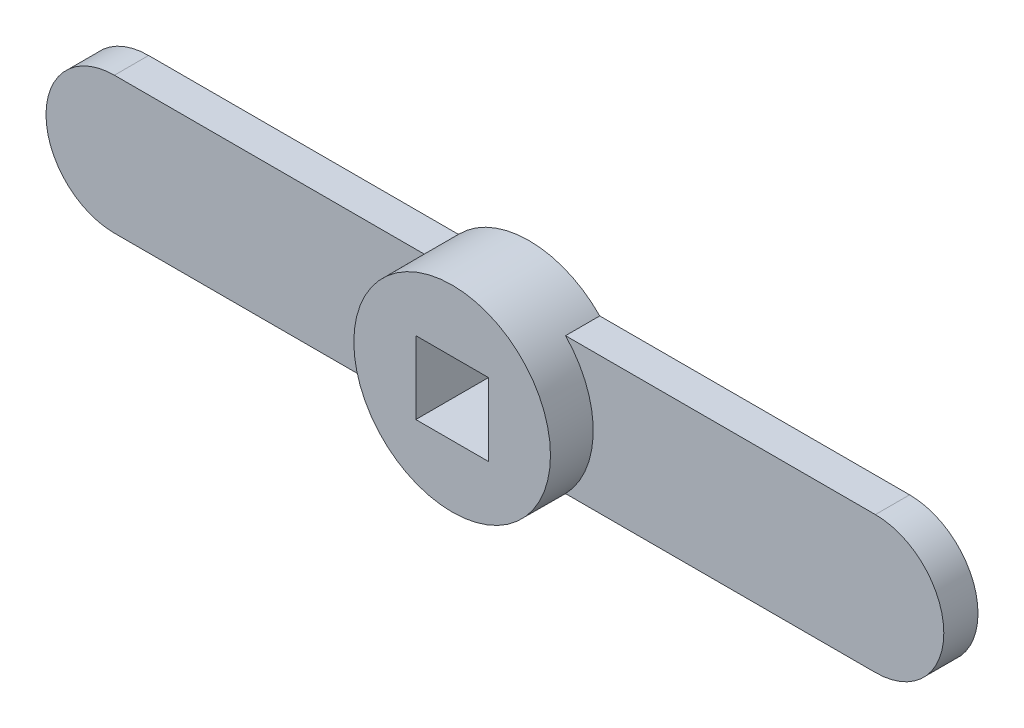
SolidWorks part; units mm, degrees
material "Сталь"
ref_plane "Спереди" through (0, 0, 0) normal (0, 0, 1) x (1, 0, 0)
ref_plane "Сверху" through (0, 0, 0) normal (0, 1, 0) x (1, 0, 0)
ref_plane "Справа" through (0, 0, 0) normal (1, 0, 0) x (0, 0, -1)
sketch "Эскиз1" plane through (0, 0, 0) normal (0, 0, 1) x (1, 0, 0)
  line L0 (-44.5, 0) -> (44.5, 0) construction
  line L1 (-44.5, 8) -> (44.5, 8)
  line L2 (-44.5, -8) -> (44.5, -8)
  arc A0 (-44.5, 8) -> (-44.5, -8) centre (-44.5, 0) ccw
  arc A1 (44.5, -8) -> (44.5, 8) centre (44.5, 0) ccw
  point P2 (0, 0)
  dimension "D2" = 105
  dimension "D1" = 16
extrude "Бобышка-Вытянуть1" add sketch "Эскиз1" along normal blind 4
sketch "Эскиз2" plane through (0, 0, 0) normal (0, 0, -1) x (-1, 0, 0)
  circle A0 centre (0, 0) radius 11.5
  dimension "D1" = 23
extrude "Бобышка-Вытянуть2" add sketch "Эскиз2" against normal blind 9
sketch "Эскиз3" plane through (0, 0, 0) normal (0, 0, -1) x (-1, 0, 0)
  line L1 (-4.25, -4.25) -> (4.25, -4.25)
  line L2 (-4.25, -4.25) -> (-4.25, 4.25)
  line L3 (-4.25, 4.25) -> (4.25, 4.25)
  line L4 (4.25, -4.25) -> (4.25, 4.25)
  line L5 (-4.25, -4.25) -> (4.25, 4.25) construction
  line L6 (-4.25, 4.25) -> (4.25, -4.25) construction
  point P0 (0, 0)
  dimension "D1" = 8.5
extrude "Вырез-Вытянуть1" cut sketch "Эскиз3" against normal through all
